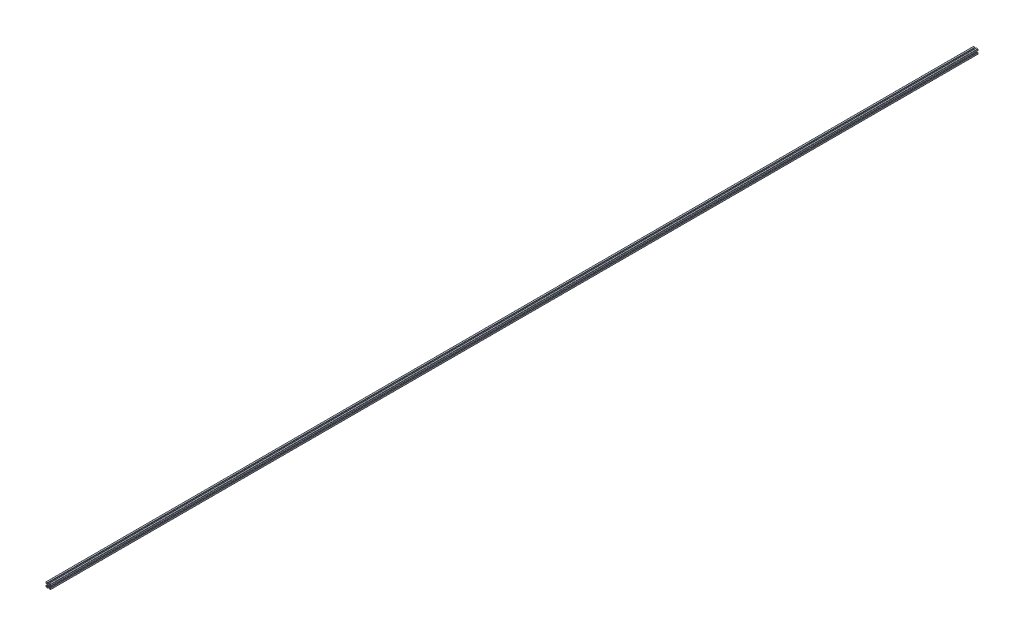
SolidWorks part; units mm, degrees
ref_plane "正面" through (0, 0, 0) normal (0, 0, 1) x (1, 0, 0)
ref_plane "平面" through (0, 0, 0) normal (0, 1, 0) x (1, 0, 0)
ref_plane "右側面" through (0, 0, 0) normal (1, 0, 0) x (0, 0, -1)
sketch "ｽｹｯﾁ2" plane through (0, 0, 0) normal (0, 0, 1) x (1, 0, 0)
  line L0 (10, 9) -> (10, 3.3)
  line L1 (0, 0) -> (12.5858, 12.5858) construction
  line L2 (55, 0) -> (-55, 0) construction
  line L3 (-4, 0.3) -> (-3.7, 0)
  line L4 (-4, 2.94) -> (-4, 0.3)
  line L5 (3.3, 10) -> (9, 10)
  line L6 (2.9399, 3.9999) -> (0.3, 3.9999)
  line L7 (-0.3, 3.9999) -> (0, 3.6999)
  line L8 (-2.9399, 3.9999) -> (-0.3, 3.9999)
  line L9 (-7.06, 6) -> (-8, 6)
  line L10 (-6, 8) -> (-6, 7.06)
  line L11 (-7.06, 6) -> (-4, 2.94)
  line L12 (-8, 6) -> (-8, 3)
  line L13 (-9.7, 3) -> (-8, 3)
  line L14 (-3, 9.7) -> (-3, 8)
  line L15 (-6, 8) -> (-3, 8)
  line L16 (-6, 7.06) -> (-2.9399, 3.9999)
  line L17 (-3.3, 10) -> (-9, 10)
  line L18 (-10, 9) -> (-10, 3.3)
  line L19 (4, -0.3) -> (3.7, 0)
  line L20 (4, -2.94) -> (4, -0.3)
  line L21 (-4, -0.3) -> (-3.7, 0)
  line L22 (-4, -2.94) -> (-4, -0.3)
  line L23 (7.06, -6) -> (8, -6)
  line L24 (6, 7.06) -> (2.9399, 3.9999)
  line L25 (6, 8) -> (3, 8)
  line L26 (3, 9.7) -> (3, 8)
  line L27 (9.7, 3) -> (8, 3)
  line L28 (8, 6) -> (8, 3)
  line L29 (7.06, 6) -> (4, 2.94)
  line L30 (6, -8) -> (6, -7.06)
  line L31 (0.3, -3.9999) -> (0, -3.6999)
  line L32 (7.06, -6) -> (4, -2.94)
  line L33 (8, -6) -> (8, -3)
  line L34 (9.7, -3) -> (8, -3)
  line L35 (3, -9.7) -> (3, -8)
  line L36 (0.3, 3.9999) -> (0, 3.6999)
  line L37 (6, -8) -> (3, -8)
  line L38 (6, 8) -> (6, 7.06)
  line L39 (6, -7.06) -> (2.9399, -3.9999)
  line L40 (-10, -9) -> (-10, -3.3)
  line L41 (-3.3, -10) -> (-9, -10)
  line L42 (-6, -7.06) -> (-2.9399, -3.9999)
  line L43 (-6, -8) -> (-3, -8)
  line L44 (7.06, 6) -> (8, 6)
  line L45 (4, 0.3) -> (3.7, 0)
  line L46 (-3, -9.7) -> (-3, -8)
  line L47 (-9.7, -3) -> (-8, -3)
  line L48 (4, 2.94) -> (4, 0.3)
  line L49 (-8, -6) -> (-8, -3)
  line L50 (-7.06, -6) -> (-4, -2.94)
  line L51 (-6, -8) -> (-6, -7.06)
  line L52 (-7.06, -6) -> (-8, -6)
  line L53 (-2.9399, -3.9999) -> (-0.3, -3.9999)
  line L54 (-0.3, -3.9999) -> (0, -3.6999)
  line L55 (2.9399, -3.9999) -> (0.3, -3.9999)
  line L56 (0, 0) -> (0, 10) construction
  line L57 (0, 0) -> (10, 0) construction
  line L58 (3.3, -10) -> (9, -10)
  line L59 (10, -9) -> (10, -3.3)
  arc A0 (-9.7, 3) -> (-10, 3.3) centre (-9.7, 3.3) cw
  arc A1 (10, 9) -> (9, 10) centre (9, 9) ccw
  arc A2 (-3.3, 10) -> (-3, 9.7) centre (-3.3, 9.7) cw
  arc A3 (-10, 9) -> (-9, 10) centre (-9, 9) cw
  arc A4 (9.7, -3) -> (10, -3.3) centre (9.7, -3.3) cw
  arc A5 (3.3, -10) -> (3, -9.7) centre (3.3, -9.7) cw
  arc A6 (-10, -9) -> (-9, -10) centre (-9, -9) ccw
  arc A7 (3.3, 10) -> (3, 9.7) centre (3.3, 9.7) ccw
  arc A8 (9.7, 3) -> (10, 3.3) centre (9.7, 3.3) ccw
  arc A9 (-3.3, -10) -> (-3, -9.7) centre (-3.3, -9.7) ccw
  arc A10 (10, -9) -> (9, -10) centre (9, -9) cw
  arc A11 (-9.7, -3) -> (-10, -3.3) centre (-9.7, -3.3) ccw
  circle A12 centre (0, 0) radius 2.1
  dimension "D8" = 2
  dimension "D9" = 4.2
  dimension "D3" = 1
  dimension "D5" = 0.3
  dimension "D17" = 0.3
  dimension "D1" = 10
  dimension "D2" = 10
  dimension "D4" = 3
  dimension "D6" = 2
  dimension "D7" = 4.0001
  dimension "D10" = 4
  dimension "D11" = 0.94
  dimension "D12" = 0.94
  dimension "D13" = 2.94
  dimension "D14" = 0.3
  dimension "D15" = 45
  dimension "D16" = 45
  dimension "D18" = 3
  dimension "D19" = 6
  dimension "D21" = 90
  dimension "D22" = 6
  dimension "D23" = 0.3
extrude "押し出し1" add sketch "ｽｹｯﾁ2" along normal blind 4000
